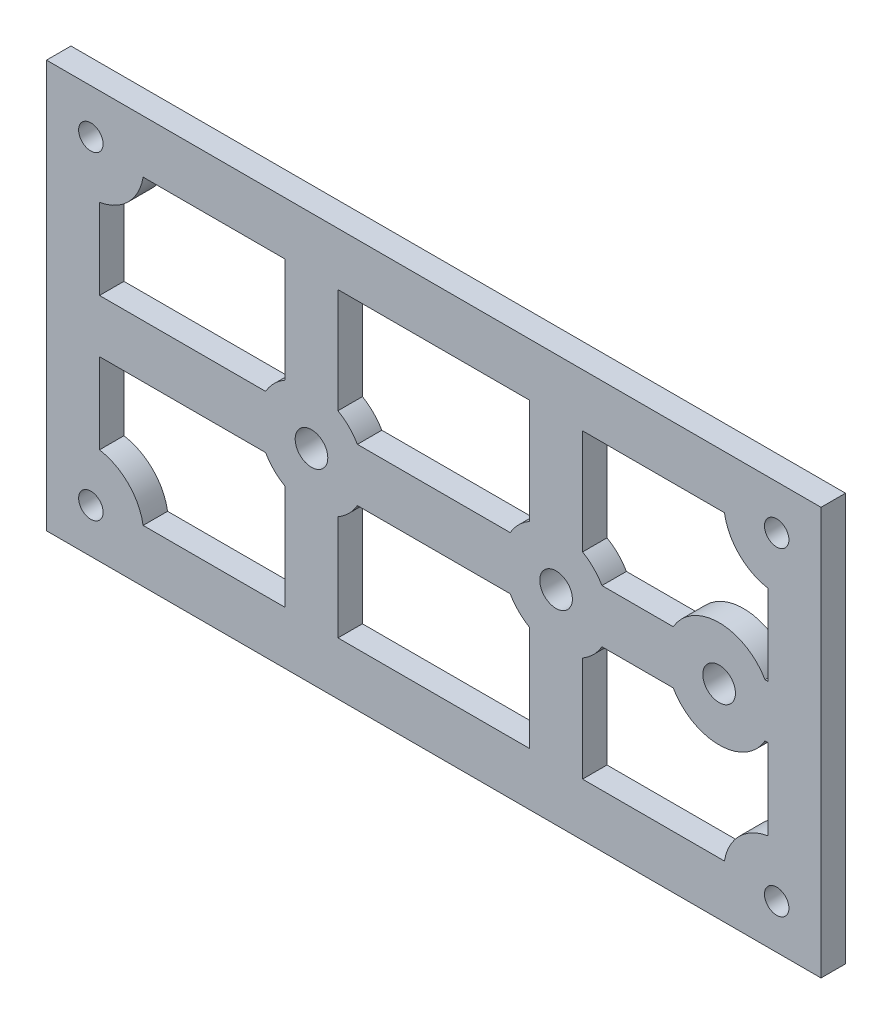
SolidWorks part; units mm, degrees
ref_plane "Front Plane" through (0, 0, 0) normal (0, 0, 1) x (1, 0, 0)
ref_plane "Top Plane" through (0, 0, 0) normal (0, 1, 0) x (1, 0, 0)
ref_plane "Right Plane" through (0, 0, 0) normal (1, 0, 0) x (0, 0, -1)
sketch "Sketch1" plane through (0, 0, 0) normal (0, 0, 1) x (1, 0, 0)
  line L0 (-47.5, 0) -> (47.5, 0) construction
  line L1 (-47.5, -25) -> (47.5, -25)
  line L2 (-47.5, -25) -> (-47.5, 25)
  line L3 (-47.5, 25) -> (47.5, 25)
  line L4 (47.5, -25) -> (47.5, 25)
  line L5 (-47.5, -25) -> (47.5, 25) construction
  line L6 (-47.5, 25) -> (47.5, -25) construction
  line L7 (-35.6478, 18.5) -> (-18.25, 18.5)
  line L8 (-41, 3.25) -> (-20.6292, 3.25)
  line L9 (-41, -3.25) -> (-20.6292, -3.25)
  line L10 (-35.6478, -18.5) -> (-18.25, -18.5)
  line L11 (-41, 13.1478) -> (-41, 3.25)
  line L12 (-18.25, 18.5) -> (-18.25, 5.6292)
  line L13 (-11.75, -18.5) -> (-11.75, -5.6292)
  line L14 (11.75, 18.5) -> (11.75, 5.6292)
  line L15 (18.25, -18.5) -> (18.25, -5.6292)
  line L16 (41, 13.1478) -> (41, 3.25)
  line L17 (0, 25) -> (0, -25) construction
  line L18 (-15, 18.5) -> (-15, -18.5) construction
  line L19 (15, 18.5) -> (15, -18.5) construction
  line L20 (-42.0607, 19.5607) -> (-42.0607, 18.0607) construction
  line L21 (-42.0607, -19.5607) -> (42.0607, -19.5607) construction
  line L22 (42.0607, -19.5607) -> (42.0607, 19.5607) construction
  line L23 (42.0607, 19.5607) -> (0, 19.5607) construction
  line L24 (-42.0607, 18.0607) -> (-42.0607, 13.0607) construction
  line L25 (-43.1213, -20.6213) -> (-41, -20.6213) construction
  line L26 (-43.1213, -20.6213) -> (-43.1213, -18.5) construction
  line L27 (-43.1213, -18.5) -> (-41, -18.5) construction
  line L28 (-41, -20.6213) -> (-41, -18.5) construction
  line L29 (-43.1213, -20.6213) -> (-41, -18.5) construction
  line L30 (-43.1213, -18.5) -> (-41, -20.6213) construction
  line L31 (-42.0607, 13.0607) -> (-42.0607, -19.5607) construction
  line L32 (-41, 18.5) -> (-41, 13.1478) construction
  line L33 (-41, 18.5) -> (-35.6478, 18.5) construction
  line L34 (-41, -18.5) -> (-35.6478, -18.5) construction
  line L35 (-41, -13.1478) -> (-41, -18.5) construction
  line L36 (41, -13.1478) -> (41, -18.5) construction
  line L37 (35.6478, -18.5) -> (41, -18.5) construction
  line L38 (41, 18.5) -> (41, 13.1478) construction
  line L39 (35.6478, 18.5) -> (41, 18.5) construction
  line L40 (41, 3.25) -> (41, 2.5) construction
  line L41 (41, -3.25) -> (41, -13.1478)
  line L42 (41, 2.5) -> (41, 0) construction
  line L43 (41, 0) -> (41, -2.5) construction
  line L44 (41, -2.5) -> (41, -3.25) construction
  line L45 (29.3708, -3.25) -> (40.6292, -3.25) construction
  line L46 (40.6292, -3.25) -> (41, -3.25)
  line L47 (29.3708, 3.25) -> (40.6292, 3.25) construction
  line L48 (40.6292, 3.25) -> (41, 3.25)
  line L49 (11.75, 3.25) -> (15, 3.25) construction
  line L50 (20.6292, 3.25) -> (29.3708, 3.25)
  line L51 (15, 3.25) -> (18.25, 3.25) construction
  line L52 (18.25, 0) -> (18.25, 3.25) construction
  line L53 (18.25, 5.6292) -> (18.25, 18.5)
  line L54 (18.25, -3.25) -> (18.25, 0) construction
  line L55 (15, -3.25) -> (18.25, -3.25) construction
  line L56 (20.6292, -3.25) -> (29.3708, -3.25)
  line L57 (11.75, -3.25) -> (15, -3.25) construction
  line L58 (11.75, 0) -> (11.75, -3.25) construction
  line L59 (11.75, -5.6292) -> (11.75, -18.5)
  line L60 (11.75, 3.25) -> (11.75, 0) construction
  line L61 (11.75, 18.5) -> (15, 18.5) construction
  line L62 (18.25, 18.5) -> (35.6478, 18.5)
  line L63 (15, 18.5) -> (18.25, 18.5) construction
  line L64 (15, -18.5) -> (18.25, -18.5) construction
  line L65 (18.25, -18.5) -> (35.6478, -18.5)
  line L66 (11.75, -18.5) -> (15, -18.5) construction
  line L67 (-11.75, 3.25) -> (-9.3708, 3.25) construction
  line L68 (-9.3708, 3.25) -> (9.3708, 3.25)
  line L69 (-11.75, 3.25) -> (-11.75, 5.6292) construction
  line L70 (-11.75, 5.6292) -> (-11.75, 18.5)
  line L71 (-15, 3.25) -> (-11.75, 3.25) construction
  line L72 (-11.75, 0) -> (-11.75, 3.25) construction
  line L73 (-11.75, -3.25) -> (-11.75, 0) construction
  line L74 (-15, -3.25) -> (-11.75, -3.25) construction
  line L75 (-9.3708, -3.25) -> (9.3708, -3.25)
  line L76 (-11.75, -5.6292) -> (-11.75, -3.25) construction
  line L77 (-11.75, -3.25) -> (-9.3708, -3.25) construction
  line L78 (-18.25, -3.25) -> (-15, -3.25) construction
  line L79 (-18.25, 0) -> (-18.25, -3.25) construction
  line L80 (-18.25, -5.6292) -> (-18.25, -18.5)
  line L81 (-20.6292, -3.25) -> (-18.25, -3.25) construction
  line L82 (-18.25, -3.25) -> (-18.25, -5.6292) construction
  line L83 (-20.6292, 3.25) -> (-18.25, 3.25) construction
  line L84 (-18.25, 3.25) -> (-15, 3.25) construction
  line L85 (-18.25, 5.6292) -> (-18.25, 3.25) construction
  line L86 (-18.25, 3.25) -> (-18.25, 0) construction
  line L87 (-18.25, -18.5) -> (-15, -18.5) construction
  line L88 (-11.75, -18.5) -> (11.75, -18.5)
  line L89 (-15, -18.5) -> (-11.75, -18.5) construction
  line L90 (-15, 18.5) -> (-11.75, 18.5) construction
  line L91 (-11.75, 18.5) -> (11.75, 18.5)
  line L92 (0, 19.5607) -> (-35.5607, 19.5607) construction
  line L93 (-35.5607, 19.5607) -> (-42.0607, 19.5607) construction
  line L94 (-18.25, 18.5) -> (-15, 18.5) construction
  line L95 (-41, 3.25) -> (-41, 0) construction
  line L96 (-41, -3.25) -> (-41, -13.1478)
  line L97 (-41, 0) -> (-41, -3.25) construction
  line L98 (18.25, -3.25) -> (20.6292, -3.25) construction
  line L99 (18.25, -5.6292) -> (18.25, -3.25) construction
  line L100 (11.75, -3.25) -> (11.75, -5.6292) construction
  line L101 (9.3708, -3.25) -> (11.75, -3.25) construction
  line L102 (18.25, 3.25) -> (20.6292, 3.25) construction
  line L103 (18.25, 3.25) -> (18.25, 5.6292) construction
  line L104 (11.75, 5.6292) -> (11.75, 3.25) construction
  line L105 (9.3708, 3.25) -> (11.75, 3.25) construction
  arc A0 (20.6292, 3.25) -> (18.25, 5.6292) centre (15, 0) ccw
  arc A1 (-9.3708, 3.25) -> (-11.75, 5.6292) centre (-15, 0) ccw
  circle A3 centre (-15, 0) radius 2
  circle A4 centre (15, 0) radius 2
  circle A5 centre (42.0607, -19.5607) radius 1.5
  arc A6 (45.6193, -25) -> (46.3852, -24.4133) centre (42.0607, -19.5607) ccw construction
  arc A7 (41, -13.1478) -> (35.6478, -18.5) centre (42.0607, -19.5607) ccw
  circle A8 centre (42.0607, 19.5607) radius 1.5
  arc A9 (46.3852, 24.4133) -> (45.6193, 25) centre (42.0607, 19.5607) ccw construction
  arc A10 (35.6478, 18.5) -> (41, 13.1478) centre (42.0607, 19.5607) ccw
  circle A11 centre (-42.0607, 19.5607) radius 1.5
  arc A12 (-45.6193, 25) -> (-46.3852, 24.4133) centre (-42.0607, 19.5607) ccw construction
  circle A13 centre (-42.0607, -19.5607) radius 1.5
  arc A14 (-46.3852, -24.4133) -> (-45.6193, -25) centre (-42.0607, -19.5607) ccw construction
  arc A15 (-47.5, 16.0021) -> (-42.0607, 13.0607) centre (-42.0607, 19.5607) ccw construction
  arc A16 (-35.6478, -18.5) -> (-41, -13.1478) centre (-42.0607, -19.5607) ccw
  arc A17 (29.3708, -3.25) -> (40.6292, -3.25) centre (35, 0) ccw
  circle A18 centre (35, 0) radius 2
  arc A19 (-38.5021, 25) -> (-45.6193, 25) centre (-42.0607, 19.5607) ccw construction
  arc A20 (-45.6193, -25) -> (-38.5021, -25) centre (-42.0607, -19.5607) ccw construction
  arc A21 (46.3852, -24.4133) -> (47.5, -23.1193) centre (42.0607, -19.5607) ccw construction
  arc A22 (-47.5, -23.1193) -> (-46.3852, -24.4133) centre (-42.0607, -19.5607) ccw construction
  arc A23 (-46.3852, 24.4133) -> (-47.5, 23.1193) centre (-42.0607, 19.5607) ccw construction
  arc A24 (47.5, 23.1193) -> (46.3852, 24.4133) centre (42.0607, 19.5607) ccw construction
  arc A25 (-42.0607, -13.0607) -> (-47.5, -16.0021) centre (-42.0607, -19.5607) ccw construction
  arc A26 (-41, -13.1478) -> (-42.0607, -13.0607) centre (-42.0607, -19.5607) ccw construction
  arc A27 (-38.5021, -25) -> (-35.5607, -19.5607) centre (-42.0607, -19.5607) ccw construction
  arc A28 (-35.5607, -19.5607) -> (-35.6123, -18.7433) centre (-42.0607, -19.5607) ccw construction
  arc A29 (-35.6123, -18.7433) -> (-35.6478, -18.5) centre (-42.0607, -19.5607) ccw construction
  arc A30 (-42.0607, 13.0607) -> (-41, 13.1478) centre (-42.0607, 19.5607) ccw construction
  arc A31 (-41, 13.1478) -> (-35.6478, 18.5) centre (-42.0607, 19.5607) ccw
  arc A32 (-35.5607, 19.5607) -> (-38.5021, 25) centre (-42.0607, 19.5607) ccw construction
  arc A33 (-35.6123, 18.7433) -> (-35.5607, 19.5607) centre (-42.0607, 19.5607) ccw construction
  arc A34 (-35.6478, 18.5) -> (-35.6123, 18.7433) centre (-42.0607, 19.5607) ccw construction
  arc A35 (38.5021, 25) -> (35.5607, 19.5607) centre (42.0607, 19.5607) ccw construction
  arc A36 (35.5607, 19.5607) -> (35.6123, 18.7433) centre (42.0607, 19.5607) ccw construction
  arc A37 (35.6123, 18.7433) -> (35.6478, 18.5) centre (42.0607, 19.5607) ccw construction
  arc A38 (41, 13.1478) -> (42.0607, 13.0607) centre (42.0607, 19.5607) ccw construction
  arc A39 (42.0607, 13.0607) -> (47.5, 16.0021) centre (42.0607, 19.5607) ccw construction
  arc A40 (47.5, -16.0021) -> (42.0607, -13.0607) centre (42.0607, -19.5607) ccw construction
  arc A41 (42.0607, -13.0607) -> (41, -13.1478) centre (42.0607, -19.5607) ccw construction
  arc A42 (35.5607, -19.5607) -> (38.5021, -25) centre (42.0607, -19.5607) ccw construction
  arc A43 (35.6123, -18.7433) -> (35.5607, -19.5607) centre (42.0607, -19.5607) ccw construction
  arc A44 (35.6478, -18.5) -> (35.6123, -18.7433) centre (42.0607, -19.5607) ccw construction
  arc A45 (28.5, 0) -> (29.3708, -3.25) centre (35, 0) ccw construction
  arc A46 (29.3708, 3.25) -> (28.5, 0) centre (35, 0) ccw construction
  arc A47 (21.5, 0) -> (20.6292, 3.25) centre (15, 0) ccw construction
  arc A48 (20.6292, -3.25) -> (21.5, 0) centre (15, 0) ccw construction
  arc A49 (9.3708, 3.25) -> (8.5, 0) centre (15, 0) ccw construction
  arc A50 (9.3708, -3.25) -> (11.75, -5.6292) centre (15, 0) ccw
  arc A51 (8.5, 0) -> (9.3708, -3.25) centre (15, 0) ccw construction
  arc A52 (15, 6.5) -> (11.75, 5.6292) centre (15, 0) ccw construction
  arc A53 (11.75, 5.6292) -> (9.3708, 3.25) centre (15, 0) ccw
  arc A54 (18.25, 5.6292) -> (15, 6.5) centre (15, 0) ccw construction
  arc A55 (15, -6.5) -> (18.25, -5.6292) centre (15, 0) ccw construction
  arc A56 (18.25, -5.6292) -> (20.6292, -3.25) centre (15, 0) ccw
  arc A57 (11.75, -5.6292) -> (15, -6.5) centre (15, 0) ccw construction
  arc A58 (-9.3708, -3.25) -> (-8.5, 0) centre (-15, 0) ccw construction
  arc A59 (-8.5, 0) -> (-9.3708, 3.25) centre (-15, 0) ccw construction
  arc A60 (-11.75, 5.6292) -> (-15, 6.5) centre (-15, 0) ccw construction
  arc A61 (-18.25, 5.6292) -> (-20.6292, 3.25) centre (-15, 0) ccw
  arc A62 (-15, 6.5) -> (-18.25, 5.6292) centre (-15, 0) ccw construction
  arc A63 (-15, -6.5) -> (-11.75, -5.6292) centre (-15, 0) ccw construction
  arc A64 (-11.75, -5.6292) -> (-9.3708, -3.25) centre (-15, 0) ccw
  arc A65 (-18.25, -5.6292) -> (-15, -6.5) centre (-15, 0) ccw construction
  arc A66 (-21.5, 0) -> (-20.6292, -3.25) centre (-15, 0) ccw construction
  arc A67 (-20.6292, -3.25) -> (-18.25, -5.6292) centre (-15, 0) ccw
  arc A68 (-20.6292, 3.25) -> (-21.5, 0) centre (-15, 0) ccw construction
  arc A69 (41.5, 0) -> (41, 2.5) centre (35, 0) ccw construction
  arc A70 (40.6292, 3.25) -> (29.3708, 3.25) centre (35, 0) ccw
  arc A71 (41, -2.5) -> (41.5, 0) centre (35, 0) ccw construction
  arc A72 (40.6292, -3.25) -> (41, -2.5) centre (35, 0) ccw construction
  arc A73 (41, 2.5) -> (40.6292, 3.25) centre (35, 0) ccw construction
  point P0 (0, 0)
  point P55 (-42.0607, -18.5)
  point P59 (-41, -19.5607)
  point P116 (0, 0)
  point P117 (46.3852, -24.4133)
  point P118 (0, 0)
  point P119 (45.6193, -25)
  point P120 (46.3852, 24.4133)
  dimension "D8" = 13
  dimension "D9" = 4
  dimension "D10" = 30
  dimension "D12" = 3
  dimension "D2" = 6.5
  dimension "D3" = 6.5
  dimension "D4" = 20
  dimension "D5" = 6.5
  dimension "D6" = 95
  dimension "D7" = 6.5
  dimension "D11" = 50
sketch "Sketch2" plane through (0, 0, 0) normal (0, 0, 1) x (1, 0, 0)
  line L0 (-47.5, 0) -> (47.5, 0) construction
  line L1 (-47.5, -25) -> (47.5, -25)
  line L2 (-47.5, -25) -> (-47.5, 25)
  line L3 (-47.5, 25) -> (47.5, 25)
  line L4 (47.5, -25) -> (47.5, 25)
  line L5 (-47.5, -25) -> (47.5, 25) construction
  line L6 (-47.5, 25) -> (47.5, -25) construction
  point P0 (0, 0)
extrude "Boss-Extrude1" add sketch "Sketch2" along normal blind 3
extrude "Cut-Extrude2" cut sketch "Sketch1" against normal through all and the other way through all contours A56 L15 L65 A7 L41 L46 A17 L56 | A70 L48 L16 A10 L62 L53 A0 L50 | A53 L14 L91 L70 A1 L68 | A64 L13 L88 L59 A50 L75 | A3 | A61 L12 L7 A31 L11 L8 | A67 L9 L96 A16 L10 L80 | A5 | A8 | A4 | A18 | A11 | A13
